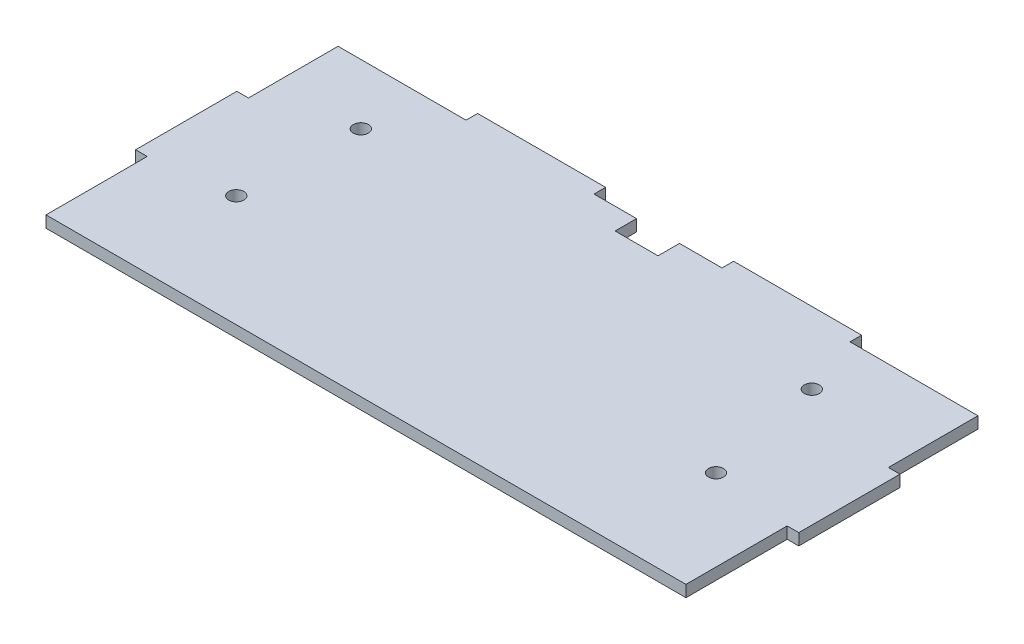
SolidWorks part; units mm, degrees
ref_plane "Front Plane" through (0, 0, 0) normal (0, 0, 1) x (1, 0, 0)
ref_plane "Top Plane" through (0, 0, 0) normal (0, 1, 0) x (1, 0, 0)
ref_plane "Right Plane" through (0, 0, 0) normal (1, 0, 0) x (0, 0, -1)
sketch "Sketch1" plane through (0, 0, 0) normal (0, 1, 0) x (1, 0, 0)
  line L0 (14.3, 49) -> (130.5961, 49) construction
  line L5 (13.3, 21) -> (124.4517, 21) construction
  line L16 (64.5, 63) -> (64.5, 58)
  line L17 (74.5, 63) -> (74.5, 58)
  line L18 (144, 18.5667) -> (144, -5)
  line L21 (74.5, -5) -> (64.5, -5)
  line L22 (74.5, 58) -> (64.5, 58)
  line L27 (-5, 18.5667) -> (-5, -5)
  line L35 (-7.7, 18.5667) -> (-5, 18.5667)
  line L39 (115.82, -5) -> (144, -5)
  line L42 (74.5, -5) -> (84.94, -5)
  line L45 (54.06, -5) -> (64.5, -5)
  line L49 (-5, -5) -> (23.18, -5)
  line L50 (-7.7, 18.5667) -> (-7.7, 42.1333)
  line L51 (-7.7, 42.1333) -> (-5, 42.1333)
  line L56 (-5, 63) -> (-5, 42.1333)
  line L64 (54.06, -5) -> (23.18, -5)
  line L65 (115.82, -5) -> (84.94, -5)
  line L67 (146.7, 18.5667) -> (146.7, 42.1333)
  line L69 (144, 63) -> (144, 42.1333)
  line L72 (146.7, 42.1333) -> (144, 42.1333)
  line L73 (146.7, 18.5667) -> (144, 18.5667)
  line L75 (24.8, 65.7) -> (54.6, 65.7)
  line L77 (84.4, 65.7) -> (114.2, 65.7)
  line L79 (-5, 63) -> (24.8, 63)
  line L80 (24.8, 65.7) -> (24.8, 63)
  line L81 (54.6, 65.7) -> (54.6, 63)
  line L82 (84.4, 65.7) -> (84.4, 63)
  line L83 (114.2, 65.7) -> (114.2, 63)
  line L84 (74.5, 63) -> (84.4, 63)
  line L85 (114.2, 63) -> (144, 63)
  line L86 (54.6, 63) -> (64.5, 63)
  circle A0 centre (13.3, 21) radius 1.75
  circle A1 centre (14.3, 49) radius 1.75
  circle A2 centre (119.3, 49) radius 1.75
  circle A3 centre (125, 21) radius 1.75
extrude "Boss-Extrude1" add sketch "Sketch1" along normal blind 2.7
